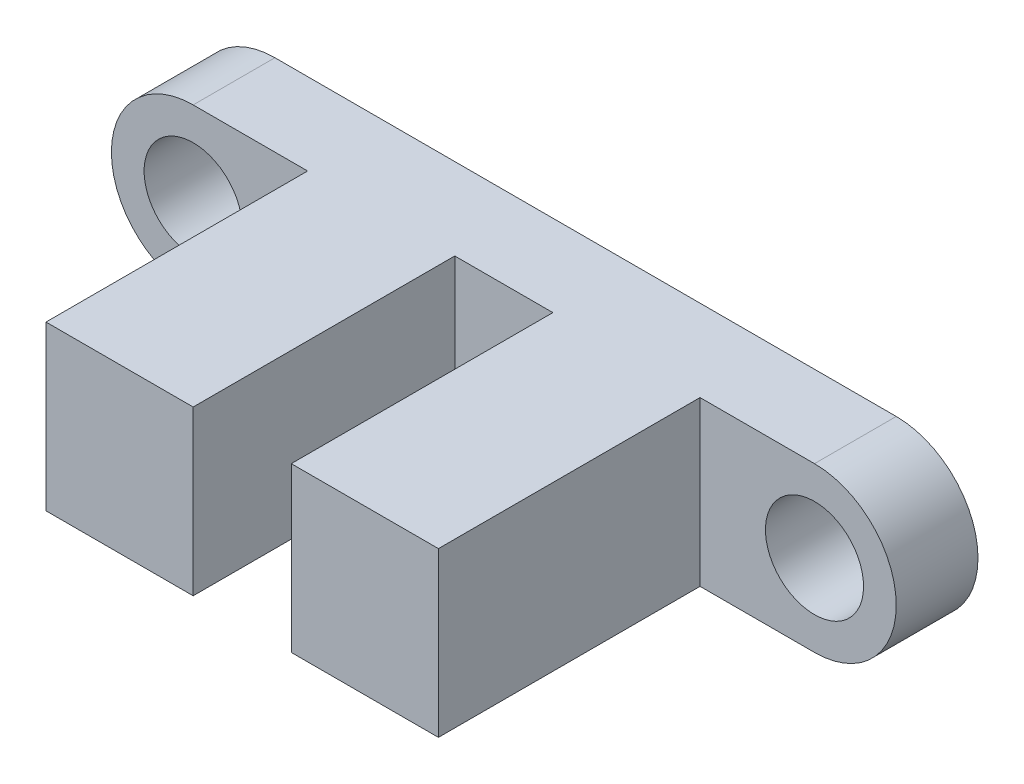
SolidWorks part; units mm, degrees
ref_plane "正面" through (0, 0, 0) normal (0, 0, 1) x (1, 0, 0)
ref_plane "平面" through (0, 0, 0) normal (0, 1, 0) x (1, 0, 0)
ref_plane "右側面" through (0, 0, 0) normal (1, 0, 0) x (0, 0, -1)
sketch "ｽｹｯﾁ1" plane through (0, 0, 0) normal (0, 0, 1) x (1, 0, 0)
  line L0 (0, 0) -> (19, 0) construction
  line L1 (0, 2.5) -> (19, 2.5)
  line L2 (0, -2.5) -> (19, -2.5)
  circle A0 centre (0, 0) radius 1.5
  circle A1 centre (19, 0) radius 1.5
  arc A2 (0, 2.5) -> (0, -2.5) centre (0, 0) ccw
  arc A3 (19, 2.5) -> (19, -2.5) centre (19, 0) cw
  dimension "D1" = 3
  dimension "D2" = 19
  dimension "D3" = 2.5
  dimension "D4" = 2.5
extrude "ﾎﾞｽ - 押し出し1" add sketch "ｽｹｯﾁ1" along normal blind 2.5
sketch "ｽｹｯﾁ2" plane through (0, 0, 2.5) normal (0, 0, 1) x (1, 0, 0)
  line L0 (9.5, 2.5) -> (9.5, -2.5) construction
  line L1 (19, 2.5) -> (0, 2.5) construction
  line L2 (0, -2.5) -> (19, -2.5) construction
  line L3 (8, 0) -> (11, 0) construction
  line L5 (8, 2.5) -> (3.5, 2.5)
  line L6 (8, 2.5) -> (8, -2.5)
  line L7 (8, -2.5) -> (3.5, -2.5)
  line L8 (3.5, 2.5) -> (3.5, -2.5)
  line L9 (15.5, 2.5) -> (11, 2.5)
  line L10 (15.5, 2.5) -> (15.5, -2.5)
  line L11 (15.5, -2.5) -> (11, -2.5)
  line L12 (11, 2.5) -> (11, -2.5)
  point P10 (9.5, 0)
  dimension "D1" = 3
  dimension "D2" = 4.5
extrude "ﾎﾞｽ - 押し出し2" add sketch "ｽｹｯﾁ2" along normal blind 8
